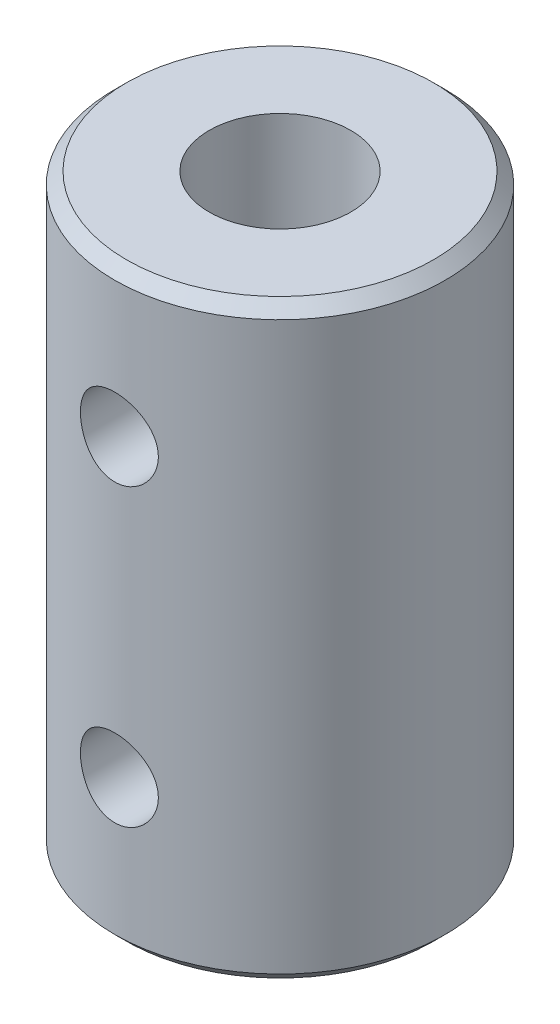
SolidWorks part; units mm, degrees
material "6061 Alloy"
ref_plane "Front Plane" through (0, 0, 0) normal (0, 0, 1) x (1, 0, 0)
ref_plane "Top Plane" through (0, 0, 0) normal (0, 1, 0) x (1, 0, 0)
ref_plane "Right Plane" through (0, 0, 0) normal (1, 0, 0) x (0, 0, -1)
sketch "Sketch2" plane through (0, 0, 0) normal (1, 0, 0) x (0, 0, -1)
  line L0 (0, 0) -> (0, 25) construction
  line L1 (4, 0) -> (4, 12.5)
  line L2 (4, 12.5) -> (3, 12.5)
  line L3 (3, 12.5) -> (3, 25)
  line L4 (3, 25) -> (7, 25)
  line L5 (7, 25) -> (7, 0)
  line L6 (7, 0) -> (4, 0)
  point P10 (3.5, 12.5)
  dimension "D1" = 25
  dimension "D2" = 7
  dimension "D3" = 4
  dimension "D4" = 3
  dimension "D5" = 12.5
revolve "Revolve1" add sketch "Sketch2" angle 360 about L0
chamfer "Chamfer1" distance 0.5 angle 45 2 edges at (0, 0, -7) (0, 25, -7)
ref_plane "Plane1" through (0, 0, 7) normal (0, 0, 1) x (1, 0, 0)
hole_wizard "M4 Tapped Hole1" positions "Sketch3" profile "Sketch4" tap size "M4" standard "ISO"
sketch "Sketch3" plane through (0, 0, 7) normal (0, 0, 1) x (1, 0, 0)
  line L0 (-6.5, 0) -> (6.5, 0) construction
  line L1 (6.5, 25) -> (-6.5, 25) construction
  point P0 (0, 18.75)
  point P2 (0, 6.25)
  dimension "D1" = 6.25
  dimension "D2" = 6.25
sketch "Sketch4" plane through (0, 18.75, 7) normal (1, 0, 0) x (0, -1, 0)
  line L0 (0, 0) -> (0, 4)
  line L1 (0, 4) -> (1.65, 4)
  line L2 (1.65, 4) -> (1.65, 0)
  line L5 (1.65, 0) -> (0, 0)
  line L11 (0, -6.35) -> (0, 107.95) construction
  dimension "Thru Tap Drill Dia." = 3.3
  dimension "Thru Tap Drill Depth" = 4
cosmetic thread "Hole Thread1" parameters "D2"=4
cosmetic thread "Hole Thread2" parameters "D2"=4
